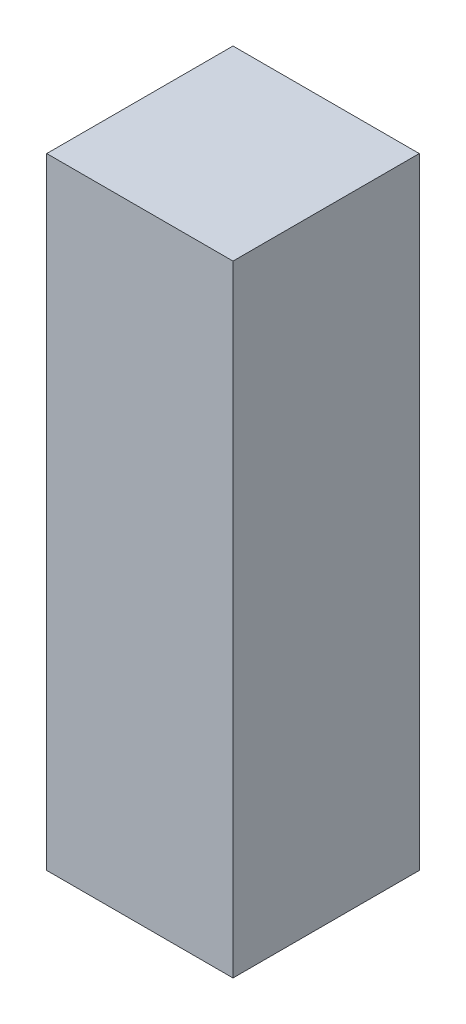
SolidWorks part; units mm, degrees
ref_plane "Front Plane" through (0, 0, 0) normal (0, 0, 1) x (1, 0, 0)
ref_plane "Top Plane" through (0, 0, 0) normal (0, 1, 0) x (1, 0, 0)
ref_plane "Right Plane" through (0, 0, 0) normal (1, 0, 0) x (0, 0, -1)
other "Bounding Box"
ref_plane "Default Plane" through (-8.9266, -12.7485, 0) normal (-0.1736, 0.9848, 0) x (0.9848, 0.1736, 0)
sketch "Sketch1" plane through (0, 0, 0) normal (0, 1, 0) x (1, 0, 0)
  line L1 (-8.5725, 8.5725) -> (8.5725, 8.5725)
  line L2 (-8.5725, 8.5725) -> (-8.5725, -8.5725)
  line L3 (-8.5725, -8.5725) -> (8.5725, -8.5725)
  line L4 (8.5725, 8.5725) -> (8.5725, -8.5725)
  line L5 (-8.5725, 8.5725) -> (8.5725, -8.5725) construction
  line L6 (-8.5725, -8.5725) -> (8.5725, 8.5725) construction
  point P0 (0, 0)
  dimension "D1" = 17.145
extrude "Boss-Extrude1" add sketch "Sketch1" along normal mid plane 57.15
